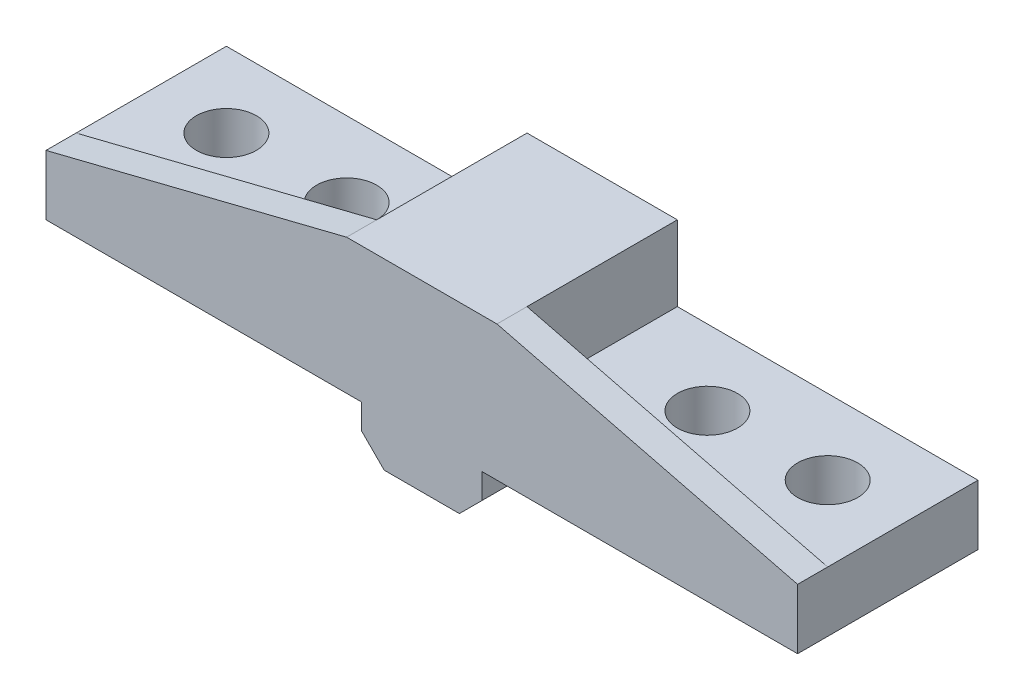
SolidWorks part; units mm, degrees
ref_plane "Front Plane" through (0, 0, 0) normal (0, 0, 1) x (1, 0, 0)
ref_plane "Top Plane" through (0, 0, 0) normal (0, 1, 0) x (1, 0, 0)
ref_plane "Right Plane" through (0, 0, 0) normal (1, 0, 0) x (0, 0, -1)
sketch "Sketch1" plane through (0, 0, 0) normal (0, 0, 1) x (1, 0, 0)
  line L0 (-25, 3.175) -> (-25, 7.175)
  line L1 (-25, 7.175) -> (-5, 7.175)
  line L2 (-5, 7.175) -> (-5, 12.175)
  line L3 (-5, 12.175) -> (5, 12.175)
  line L7 (4, 0) -> (-4, 0)
  line L8 (-4, 0) -> (-4, 3.175)
  line L9 (-4, 3.175) -> (-25, 3.175)
  line L10 (0, 12.175) -> (0, 0) construction
  line L11 (4, 3.175) -> (25, 3.175)
  line L12 (4, 0) -> (4, 3.175)
  line L13 (5, 7.175) -> (5, 12.175)
  line L14 (25, 7.175) -> (5, 7.175)
  line L15 (25, 3.175) -> (25, 7.175)
  line L16 (-25, 7.175) -> (2.2456, 26.2526) construction
  dimension "D1" = 20
  dimension "D2" = 3.175
  dimension "D3" = 5
  dimension "D4" = 4
  dimension "D5" = 4
  dimension "D6" = 25
  dimension "D7" = 35
extrude "Boss-Extrude1" add sketch "Sketch1" along normal blind 10
sketch "Sketch2" plane through (0, 0, 10) normal (0, 0, 1) x (1, 0, 0)
  line L0 (-5, 12.175) -> (-25, 7.175)
  line L1 (-25, 7.175) -> (-25, 3.175)
  line L3 (25, 3.175) -> (25, 7.175)
  line L4 (25, 7.175) -> (5, 12.175)
  line L5 (5, 12.175) -> (-5, 12.175)
  line L6 (25, 3.175) -> (4, 3.175)
  line L7 (4, 3.175) -> (4, 0)
  line L8 (4, 0) -> (-4, 0)
  line L9 (-4, 0) -> (-4, 3.175)
  line L10 (-4, 3.175) -> (-25, 3.175)
extrude "Boss-Extrude2" add sketch "Sketch2" along normal blind 2
ref_plane "Plane1" through (0, 0, 5) normal (0, 0, -1) x (-1, 0, 0)
sketch "Sketch3" plane through (0, 7.175, 0) normal (0, 1, 0) x (1, 0, 0)
  line L0 (6.6963, -5) -> (-6.6963, -5) construction
  line L1 (25, -10) -> (25, 0) construction
  line L2 (0, 0) -> (0, -12) construction
  line L3 (5, -12) -> (-5, -12) construction
  circle A0 centre (12, -5) radius 2
  circle A1 centre (20, -5) radius 2
  circle A2 centre (-12, -5) radius 2
  circle A3 centre (-20, -5) radius 2
  point P15 (0, -8)
  dimension "D1" = 4
  dimension "D2" = 5
  dimension "D3" = 8
extrude "Cut-Extrude1" cut sketch "Sketch3" against normal up to surface (4 mm away) up to face at (-14.5, 3.175, 6)
chamfer "Chamfer1" distance 1.5 angle 45 2 edges at (-4, 0, 6) (4, 0, 6)
